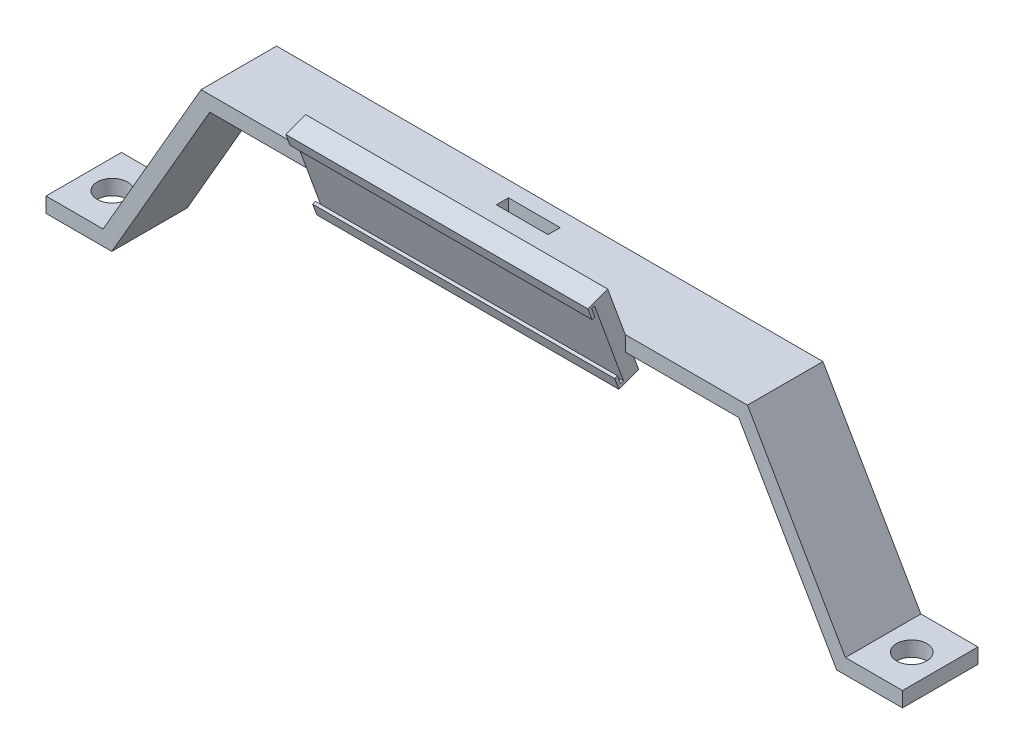
SolidWorks part; units mm, degrees
ref_plane "Front Plane" through (0, 0, 0) normal (0, 0, 1) x (1, 0, 0)
ref_plane "Top Plane" through (0, 0, 0) normal (0, 1, 0) x (1, 0, 0)
ref_plane "Right Plane" through (0, 0, 0) normal (1, 0, 0) x (0, 0, -1)
sketch "Sketch1" plane through (0, 0, 0) normal (0, 0, 1) x (1, 0, 0)
  line L0 (0, 0) -> (0, 60) construction
  line L1 (-87.5722, 56.1666) -> (87.5722, 56.1666)
  line L2 (-120, 0) -> (-126.7935, 0)
  line L3 (-90.4589, 61.1666) -> (90.4589, 61.1666)
  line L4 (92.4278, 56.1666) -> (92.4278, 61.1666)
  line L5 (0, 60) -> (0, 61.1666) construction
  line L6 (-126.7935, 0) -> (-141.7935, 0)
  line L7 (120, 0) -> (-120, 0) construction
  line L8 (-120, 0) -> (-87.5722, 56.1666)
  line L9 (-90.4589, 61.1666) -> (-122.8868, 5)
  line L10 (-141.7935, 0) -> (-141.7935, 5)
  line L11 (-141.7935, 5) -> (-122.8868, 5)
  line L12 (141.7935, 5) -> (122.8868, 5)
  line L13 (141.7935, 0) -> (141.7935, 5)
  line L14 (90.4589, 61.1666) -> (122.8868, 5)
  line L15 (120, 0) -> (87.5722, 56.1666)
  line L16 (126.7935, 0) -> (141.7935, 0)
  line L17 (120, 0) -> (126.7935, 0)
  point P0 (0, 60)
  point P22 (0, 56.1666)
  dimension "D1" = 5
  dimension "D2" = 180
  dimension "D3" = 120
  dimension "D4" = 60
  dimension "D5" = 120
  dimension "D6" = 5
  dimension "D7" = 5
  dimension "D8" = 15
extrude "Boss-Extrude1" add sketch "Sketch1" along normal blind 25
sketch "Sketch2" plane through (0, 5, 0) normal (0, 1, 0) x (1, 0, 0)
  line L0 (132.3401, -25) -> (132.3401, 0) construction
  line L1 (141.7935, -25) -> (122.8868, -25) construction
  line L2 (141.7935, 0) -> (122.8868, 0) construction
  line L3 (0, 0) -> (0, 97.8511) construction
  line L5 (-8.5486, -9.1286) -> (8.5486, -9.1286)
  line L6 (-8.5486, -9.1286) -> (-8.5486, -5.1079)
  line L7 (-8.5486, -5.1079) -> (8.5486, -5.1079)
  line L8 (8.5486, -9.1286) -> (8.5486, -5.1079)
  line L9 (-8.5486, -9.1286) -> (8.5486, -5.1079) construction
  line L10 (-8.5486, -5.1079) -> (8.5486, -9.1286) construction
  circle A0 centre (132.3401, -12.5) radius 5
  circle A1 centre (-132.3401, -12.5) radius 5
  point P13 (0, -7.1182)
  dimension "D1" = 10
extrude "Cut-Extrude1" cut sketch "Sketch2" against normal mid plane 200
sketch "Sketch3" plane through (0, 0, 0) normal (1, 0, 0) x (0, 0, -1)
  line L0 (-30.8085, 77.1253) -> (-20.5479, 48.9345)
  line L1 (-25, 61.1666) -> (0, 61.1666) construction
  line L2 (-35.1649, 74.4755) -> (-25.5884, 48.1641)
  line L3 (-35.5069, 75.4152) -> (-30.8085, 77.1253)
  line L4 (-25.2463, 47.2244) -> (-20.5479, 48.9345)
  line L5 (-20.5479, 48.9345) -> (-30.8085, 77.1253) construction
  line L6 (-35.5069, 75.4152) -> (-37.3863, 74.7311)
  line L7 (-37.3863, 74.7311) -> (-36.0182, 70.9724)
  line L8 (-36.0182, 70.9724) -> (-35.0786, 71.3144)
  line L9 (-35.0786, 71.3144) -> (-36.1046, 74.1335)
  line L10 (-36.1046, 74.1335) -> (-35.1649, 74.4755)
  line L11 (-30.2056, 60.8499) -> (-25.5072, 62.56) construction
  line L12 (-25.2463, 47.2244) -> (-27.1257, 46.5403)
  line L13 (-27.1257, 46.5403) -> (-28.4938, 50.2991)
  line L14 (-28.4938, 50.2991) -> (-27.5541, 50.6411)
  line L15 (-27.5541, 50.6411) -> (-26.5281, 47.8221)
  line L16 (-26.5281, 47.8221) -> (-25.5884, 48.1641)
  point P0 (-25, 61.1666)
  dimension "D1" = 110
  dimension "D2" = 5
  dimension "D3" = 30
  dimension "D4" = 1
  dimension "D5" = 2
  dimension "D6" = 4
  dimension "D7" = 1
  dimension "D8" = 1
  dimension "D9" = 1
  dimension "D10" = 1
  dimension "D11" = 4
extrude "Boss-Extrude2" add sketch "Sketch3" along normal mid plane 100
